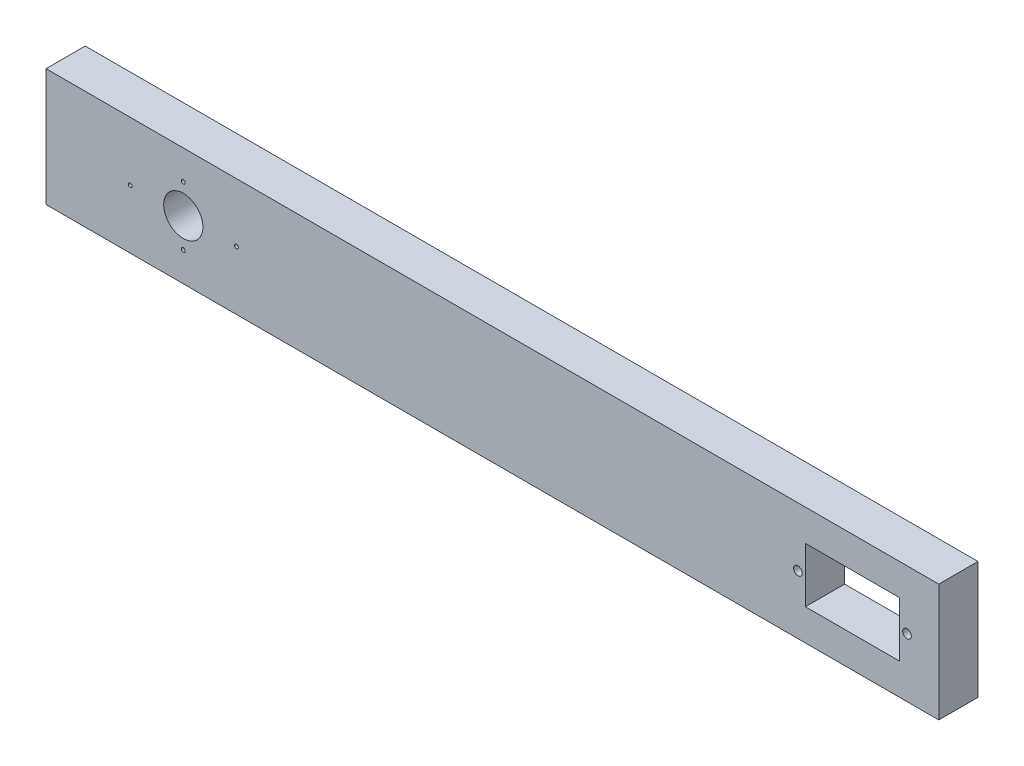
SolidWorks part; units mm, degrees
ref_plane "Front Plane" through (0, 0, 0) normal (0, 0, 1) x (1, 0, 0)
ref_plane "Top Plane" through (0, 0, 0) normal (0, 1, 0) x (1, 0, 0)
ref_plane "Right Plane" through (0, 0, 0) normal (1, 0, 0) x (0, 0, -1)
sketch "Sketch1" plane through (0, 0, 0) normal (0, 0, 1) x (1, 0, 0)
  line L0 (0, 15) -> (70, 15) construction
  line L1 (0, 30) -> (70, 30)
  line L2 (0, 30) -> (0, 0)
  line L3 (0, 0) -> (70, 0)
  line L4 (70, 30) -> (70, 0)
  line L5 (0, 30) -> (70, 0) construction
  line L6 (0, 0) -> (70, 30) construction
  line L7 (35, 30) -> (35, -55.9922) construction
  line L8 (205.6, 8) -> (205.6, 22) construction
  line L9 (70, 30) -> (227.6, 30)
  line L10 (70, 30) -> (70, 0)
  line L11 (70, 0) -> (227.6, 0)
  line L12 (227.6, 30) -> (227.6, 0)
  line L13 (193.6, 15) -> (217.6, 15) construction
  line L14 (193.6, 22) -> (217.6, 22)
  line L19 (193.6, 22) -> (193.6, 8)
  line L20 (193.6, 8) -> (217.6, 8)
  line L21 (217.6, 22) -> (217.6, 8)
  line L22 (193.6, 22) -> (217.6, 8) construction
  line L23 (193.6, 8) -> (217.6, 22) construction
  line L24 (210, 22) -> (210, 8)
  circle A0 centre (21.47, 15) radius 0.5
  circle A1 centre (35, 22.53) radius 0.5
  circle A2 centre (35, 7.47) radius 0.5
  circle A3 centre (48.53, 15) radius 0.5
  circle A8 centre (35, 15) radius 5
  circle A9 centre (219.5, 15) radius 1.1
  circle A10 centre (191.7, 15) radius 1.1
  point P0 (35, 15)
  point P22 (35, -12.9961)
  point P27 (205.6, 15)
  dimension "D4" = 1
  dimension "D6" = 1
  dimension "D10" = 13.9
  dimension "D13" = 10
  dimension "D9" = 2.2
  dimension "D1" = 30
  dimension "D2" = 70
  dimension "D3" = 13.53
  dimension "D5" = 7.53
  dimension "D7" = 24
  dimension "D8" = 14
  dimension "D12" = 15
  dimension "D14" = 16.4
  dimension "D15" = 175
  dimension "D16" = 10
extrude "Boss-Extrude1" add sketch "Sketch1" along normal blind 10
